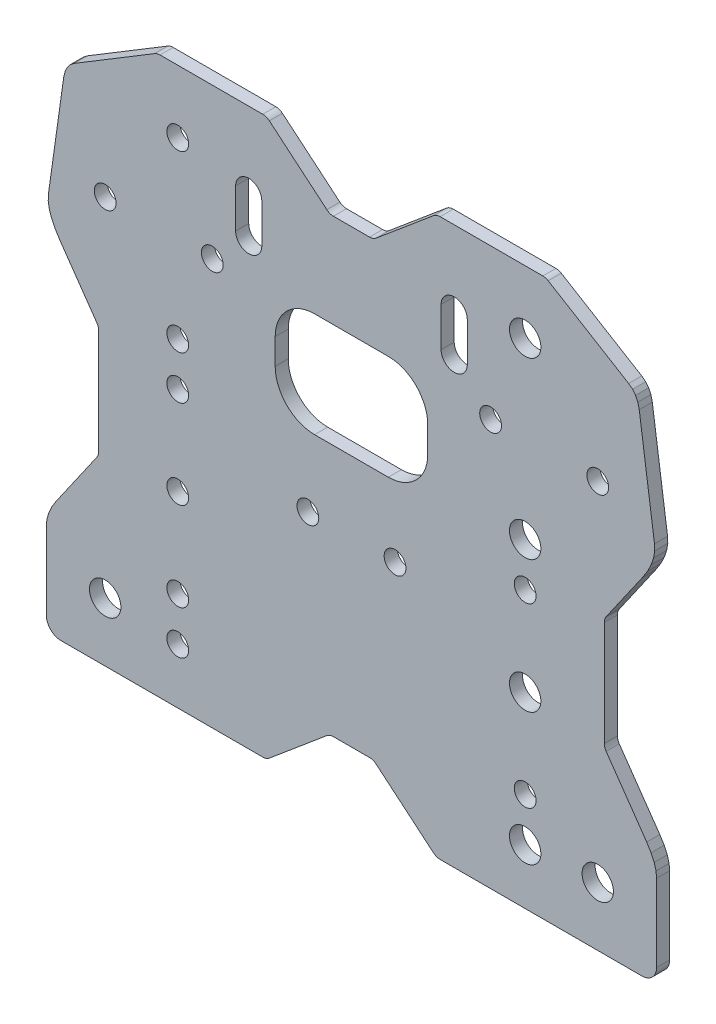
SolidWorks part; units mm, degrees
ref_plane "Front" through (0, 0, 0) normal (0, 0, 1) x (1, 0, 0)
ref_plane "Top" through (0, 0, 0) normal (0, 1, 0) x (1, 0, 0)
ref_plane "Right" through (0, 0, 0) normal (1, 0, 0) x (0, 0, -1)
sketch "Model" plane through (0, 0, 0) normal (0, 0, 1) x (1, 0, 0)
  line L0 (-63.589, 104.0453) -> (-64.492, 103.3464)
  line L1 (-64.492, 103.3464) -> (-65.1953, 102.4641)
  line L2 (-65.1953, 102.4641) -> (-65.7069, 101.3761)
  line L3 (-65.7069, 101.3761) -> (-66.0181, 100.0511)
  line L4 (-63.589, 104.0453) -> (-45.1299, 115.221)
  line L5 (-70, 8.9513) -> (-70, -8.7999)
  line L6 (-69.5178, 75.1491) -> (-66.0181, 100.0511)
  line L7 (-70, 8.9513) -> (-69.8676, 10.3299)
  line L8 (-69.8676, 10.3299) -> (-69.4502, 11.8169)
  line L9 (-69.4502, 11.8169) -> (-68.7375, 13.3804)
  line L10 (-68.7375, 13.3804) -> (-67.7332, 15.0023)
  line L11 (-66.6407, -12.1592) -> (-20.3461, -12.1592)
  line L12 (20.3461, -12.1592) -> (66.64, -12.1592)
  line L13 (-58.0056, 29.7059) -> (-58.0056, 53.777)
  line L14 (4.1447, 0) -> (-4.1447, 0)
  line L15 (-58.4279, 55.1211) -> (-66.786, 67.1087)
  line L16 (-66.786, 67.1087) -> (-67.9224, 68.903)
  line L17 (-67.9224, 68.903) -> (-68.7716, 70.6215)
  line L18 (-68.7716, 70.6215) -> (-69.3214, 72.2521)
  line L19 (-69.3214, 72.2521) -> (-69.5655, 73.7682)
  line L20 (-69.5655, 73.7682) -> (-69.5178, 75.1491)
  line L21 (-67.7332, 15.0023) -> (-58.4273, 28.3627)
  line L22 (5.6552, 103.9513) -> (18.8356, 115.011)
  line L23 (18.8356, -11.6094) -> (5.6552, -0.5498)
  line L24 (-26.57, 98.2408) -> (-26.57, 89.2408)
  line L25 (-20.57, 89.2408) -> (-20.57, 98.2408)
  line L26 (-17.5, 72.8002) -> (-17.5, 66.8999)
  line L27 (-8.4501, 57.85) -> (8.4502, 57.85)
  line L28 (17.5, 66.8999) -> (17.5, 72.8002)
  line L29 (20.57, 98.2408) -> (20.57, 89.2408)
  line L30 (26.57, 89.2408) -> (26.57, 98.2408)
  line L31 (8.4502, 81.85) -> (-8.4501, 81.85)
  line L32 (-5.6552, -0.5498) -> (-18.8356, -11.6094)
  line L33 (-18.8356, 115.011) -> (-5.6552, 103.9513)
  line L34 (58.4313, 28.3659) -> (67.7344, 15.0023)
  line L35 (66.7835, 67.1087) -> (58.432, 55.124)
  line L36 (-4.1447, 103.4016) -> (4.1447, 103.4016)
  line L37 (58.01, 53.7804) -> (58.01, 29.7086)
  line L38 (43.9128, 115.5608) -> (20.3461, 115.5608)
  line L39 (-20.3461, 115.5608) -> (-43.9128, 115.5608)
  line L40 (70, 8.9513) -> (69.8677, 10.3299)
  line L41 (69.8677, 10.3299) -> (69.4505, 11.8169)
  line L42 (69.4505, 11.8169) -> (68.7382, 13.3804)
  line L43 (68.7382, 13.3804) -> (67.7344, 15.0023)
  line L44 (69.5187, 75.1491) -> (69.5658, 73.7686)
  line L45 (69.5658, 73.7686) -> (69.3211, 72.2544)
  line L46 (69.3211, 72.2544) -> (68.771, 70.6249)
  line L47 (68.771, 70.6249) -> (67.9211, 68.9055)
  line L48 (67.9211, 68.9055) -> (66.7835, 67.1087)
  line L49 (70, -8.7992) -> (70, 8.9513)
  line L50 (66.019, 100.0511) -> (65.6988, 101.4016)
  line L51 (65.6988, 101.4016) -> (65.1722, 102.5017)
  line L52 (65.1722, 102.5017) -> (64.4748, 103.3634)
  line L53 (64.4748, 103.3634) -> (63.589, 104.0453)
  line L54 (66.019, 100.0511) -> (69.5187, 75.1491)
  line L55 (45.1299, 115.221) -> (63.589, 104.0453)
  circle A0 centre (-56.5, 1.3608) radius 3.6
  arc A1 (-70, -8.7999) -> (-66.6407, -12.1592) centre (-66.6407, -8.7999) ccw
  circle A2 centre (-10, 41.7408) radius 2.5
  circle A3 centre (-39.85, 0.5228) radius 2.5
  circle A4 centre (-39.85, 10.5228) radius 2.5
  circle A5 centre (-39.85, 30.8428) radius 2.5
  circle A6 centre (-39.85, 51.1628) radius 2.5
  arc A7 (-4.1447, 0) -> (-5.6552, -0.5498) centre (-4.1447, -2.35) ccw
  arc A8 (-58.4273, 28.3627) -> (-58.0056, 29.7059) centre (-60.3556, 29.7059) ccw
  arc A9 (-20.3461, -12.1592) -> (-18.8356, -11.6094) centre (-20.3461, -9.8092) ccw
  arc A10 (-8.4501, 81.85) -> (-17.5, 72.8002) centre (-8.4501, 72.8002) ccw
  arc A11 (-17.5, 66.8999) -> (-8.4501, 57.85) centre (-8.4501, 66.8999) ccw
  arc A12 (-20.57, 98.2408) -> (-26.57, 98.2408) centre (-23.57, 98.2408) ccw
  arc A13 (-26.57, 89.2408) -> (-20.57, 89.2408) centre (-23.57, 89.2408) ccw
  circle A14 centre (-31.925, 81.0608) radius 2.5
  circle A15 centre (-39.85, 61.1628) radius 2.5
  circle A16 centre (-39.85, 101.1628) radius 2.5
  circle A17 centre (-56.5, 81.0608) radius 2.5
  arc A18 (-58.0056, 53.777) -> (-58.4279, 55.1211) centre (-60.3556, 53.777) ccw
  arc A19 (-5.6552, 103.9513) -> (-4.1447, 103.4016) centre (-4.1447, 105.7516) ccw
  arc A20 (-18.8356, 115.011) -> (-20.3461, 115.5608) centre (-20.3461, 113.2108) ccw
  arc A21 (-43.9128, 115.5608) -> (-45.1299, 115.221) centre (-43.9128, 113.2108) ccw
  circle A22 centre (39.85, 0.5228) radius 3.6
  circle A23 centre (39.85, 30.8428) radius 3.6
  circle A24 centre (56.5, 1.3608) radius 3.6
  arc A25 (66.64, -12.1592) -> (70, -8.7992) centre (66.64, -8.7992) ccw
  circle A26 centre (10, 41.7408) radius 2.5
  circle A27 centre (39.85, 10.5228) radius 2.5
  circle A28 centre (39.85, 51.1628) radius 2.5
  arc A29 (5.6552, -0.5498) -> (4.1447, 0) centre (4.1447, -2.35) ccw
  arc A30 (58.01, 29.7086) -> (58.4313, 28.3659) centre (60.36, 29.7086) ccw
  arc A31 (18.8356, -11.6094) -> (20.3461, -12.1592) centre (20.3461, -9.8092) ccw
  arc A32 (8.4502, 57.85) -> (17.5, 66.8999) centre (8.4502, 66.8999) ccw
  arc A33 (17.5, 72.8002) -> (8.4502, 81.85) centre (8.4502, 72.8002) ccw
  circle A34 centre (39.85, 61.1628) radius 3.6
  circle A35 centre (39.85, 101.1628) radius 3.6
  arc A36 (26.57, 98.2408) -> (20.57, 98.2408) centre (23.57, 98.2408) ccw
  arc A37 (20.57, 89.2408) -> (26.57, 89.2408) centre (23.57, 89.2408) ccw
  circle A38 centre (31.925, 81.0608) radius 2.5
  circle A39 centre (56.5, 81.0608) radius 2.5
  arc A40 (58.432, 55.124) -> (58.01, 53.7804) centre (60.36, 53.7804) ccw
  arc A41 (4.1447, 103.4016) -> (5.6552, 103.9513) centre (4.1447, 105.7516) ccw
  arc A42 (20.3461, 115.5608) -> (18.8356, 115.011) centre (20.3461, 113.2108) ccw
  arc A43 (45.1299, 115.221) -> (43.9128, 115.5608) centre (43.9128, 113.2108) ccw
extrude "Boss-Extrude1" add sketch "Model" along normal blind 3
